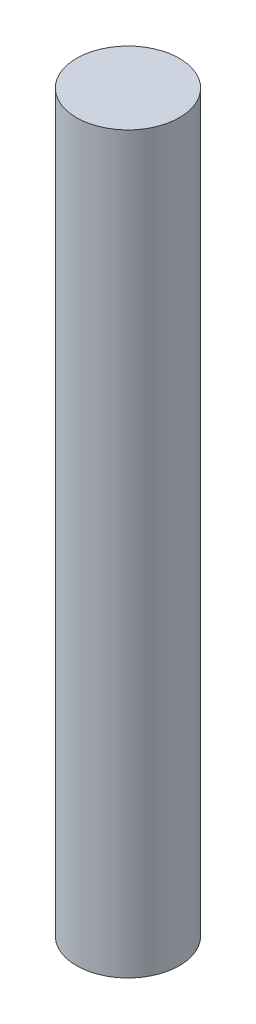
SolidWorks part; units mm, degrees
ref_plane "Front Plane" through (0, 0, 0) normal (0, 0, 1) x (1, 0, 0)
ref_plane "Top Plane" through (0, 0, 0) normal (0, 1, 0) x (1, 0, 0)
ref_plane "Right Plane" through (0, 0, 0) normal (1, 0, 0) x (0, 0, -1)
sketch "Sketch1" plane through (0, 0, 0) normal (0, 1, 0) x (1, 0, 0)
  circle A0 centre (-56.8402, 24.1081) radius 3.5
extrude "Boss-Extrude1" add sketch "Sketch1" along normal blind 50
